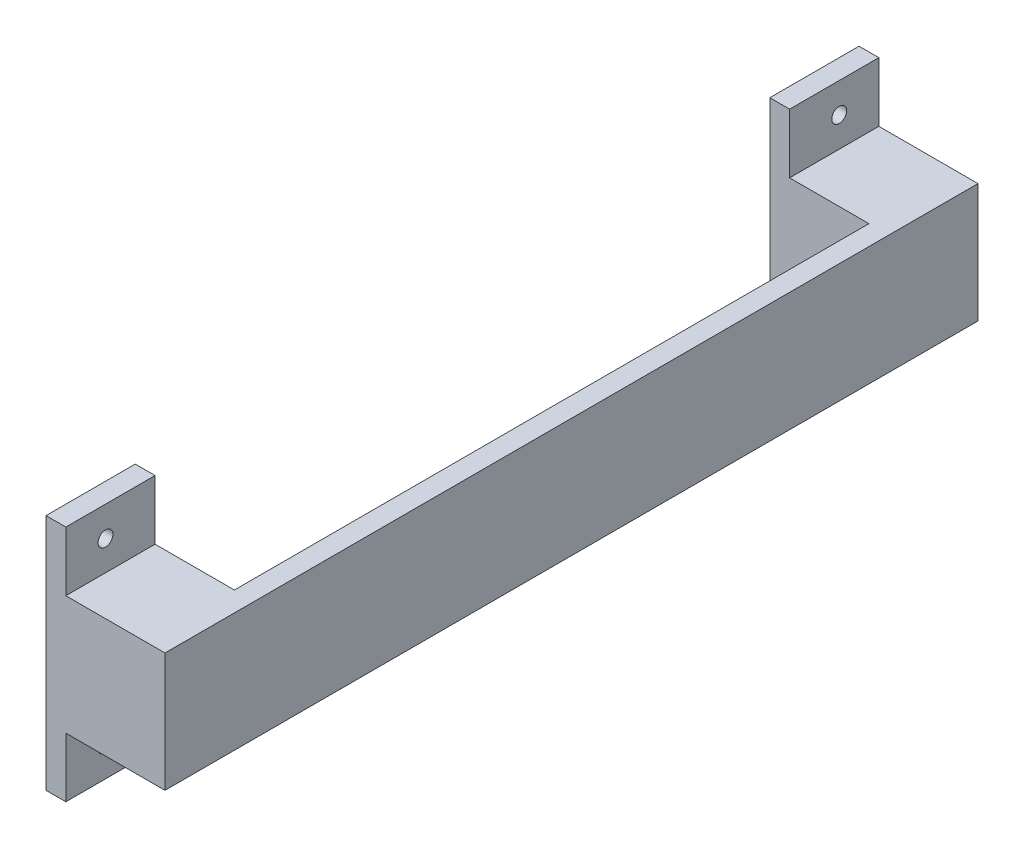
SolidWorks part; units mm, degrees
material "ABS"
ref_plane "Front Plane" through (0, 0, 0) normal (0, 0, 1) x (1, 0, 0)
ref_plane "Top Plane" through (0, 0, 0) normal (0, 1, 0) x (1, 0, 0)
ref_plane "Right Plane" through (0, 0, 0) normal (1, 0, 0) x (0, 0, -1)
sketch "Sketch1" plane through (0, 0, 0) normal (1, 0, 0) x (0, 0, -1)
  line L1 (-65.0875, 9.525) -> (65.0875, 9.525)
  line L2 (-65.0875, 9.525) -> (-65.0875, -9.525)
  line L3 (-65.0875, -9.525) -> (65.0875, -9.525)
  line L4 (65.0875, 9.525) -> (65.0875, -9.525)
  line L5 (-65.0875, 9.525) -> (65.0875, -9.525) construction
  line L6 (-65.0875, -9.525) -> (65.0875, 9.525) construction
  point P0 (0, 0)
  dimension "D1" = 130.175
  dimension "D2" = 19.05
extrude "Boss-Extrude1" add sketch "Sketch1" along normal blind 19.05
sketch "Sketch2" plane through (0, 0, 65.0875) normal (0, 0, 1) x (1, 0, 0)
  line L1 (0, 19.05) -> (3.175, 19.05)
  line L2 (0, 19.05) -> (0, -19.05)
  line L3 (0, -19.05) -> (3.175, -19.05)
  line L4 (3.175, 19.05) -> (3.175, -19.05)
  point P4 (0, 0)
  dimension "D1" = 38.1
  dimension "D2" = 3.175
extrude "Boss-Extrude2" add sketch "Sketch2" against normal up to surface (130.175 mm away) up to face at (9.525, 0, -65.0875)
sketch "Sketch4" plane through (3.175, 0, 0) normal (1, 0, 0) x (0, 0, -1)
  line L0 (-65.0875, 0) -> (65.0875, 0) construction
  line L1 (-65.0875, 9.525) -> (-65.0875, -9.525) construction
  line L2 (65.0875, -9.525) -> (65.0875, 9.525) construction
  line L3 (-65.0875, -14.2875) -> (65.0875, -14.2875) construction
  line L4 (-65.0875, -19.05) -> (-65.0875, -9.525) construction
  line L5 (65.0875, -9.525) -> (65.0875, -19.05) construction
  line L6 (0, 19.05) -> (0, -19.05) construction
  line L7 (65.0875, 19.05) -> (-65.0875, 19.05) construction
  line L8 (65.0875, -19.05) -> (-65.0875, -19.05) construction
  circle A0 centre (-58.7375, -14.2875) radius 1.1906
  circle A1 centre (58.7375, -14.2875) radius 1.1906
  circle A2 centre (58.7375, 14.2875) radius 1.1906
  circle A3 centre (-58.7375, 14.2875) radius 1.1906
  dimension "D1" = 6.35
  dimension "D2" = 2.3813
extrude "Cut-Extrude1" cut sketch "Sketch4" against normal through all
sketch "Sketch5" plane through (0, -19.05, 0) normal (0, -1, 0) x (-1, 0, 0)
  line L0 (0, 65.0875) -> (0, -65.0875) construction
  line L1 (0, -50.8) -> (-15.875, -50.8)
  line L2 (0, -50.8) -> (0, 50.8)
  line L3 (0, 50.8) -> (-15.875, 50.8)
  line L4 (-15.875, -50.8) -> (-15.875, 50.8)
  line L5 (0, 0) -> (14.3971, 0) construction
  line L6 (-19.05, -65.0875) -> (-19.05, 65.0875) construction
  dimension "D1" = 50.8
  dimension "D2" = 50.8
  dimension "D3" = 3.175
extrude "Cut-Extrude2" cut sketch "Sketch5" against normal through all
